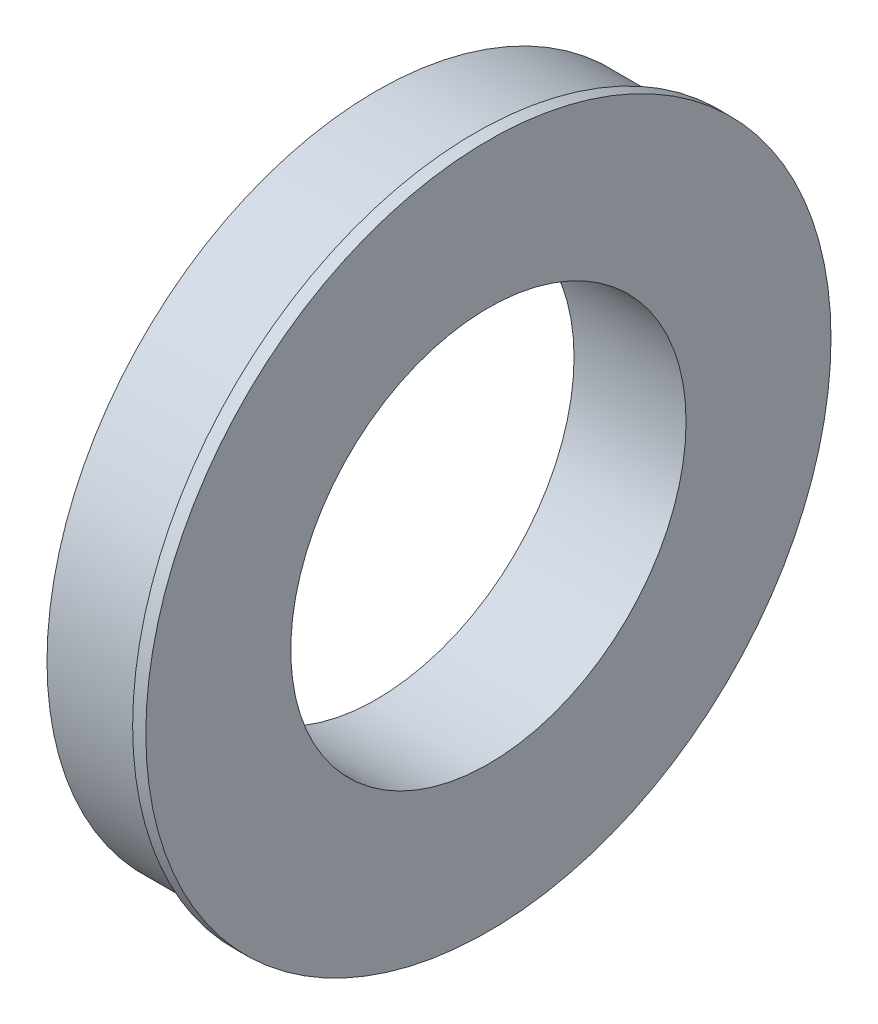
SolidWorks part; units mm, degrees
ref_plane "Front Plane" through (0, 0, 0) normal (0, 0, 1) x (1, 0, 0)
ref_plane "Top Plane" through (0, 0, 0) normal (0, 1, 0) x (1, 0, 0)
ref_plane "Right Plane" through (0, 0, 0) normal (1, 0, 0) x (0, 0, -1)
sketch "Sketch1" plane through (0, 0, 0) normal (1, 0, 0) x (0, 0, -1)
  circle A0 centre (0, 0) radius 63.5
  circle A1 centre (0, 0) radius 38.1
  dimension "D1" = 127
  dimension "D2" = 76.2
extrude "Boss-Extrude1" add sketch "Sketch1" along normal blind 19.05
sketch "Sketch2" plane through (19.05, 0, 0) normal (1, 0, 0) x (0, 0, -1)
  circle A0 centre (0, 0) radius 38.1 construction
  circle A1 centre (0, 0) radius 38.1
  circle A2 centre (0, 0) radius 66.04
  dimension "D1" = 132.08
extrude "Boss-Extrude2" add sketch "Sketch2" along normal blind 2.54
